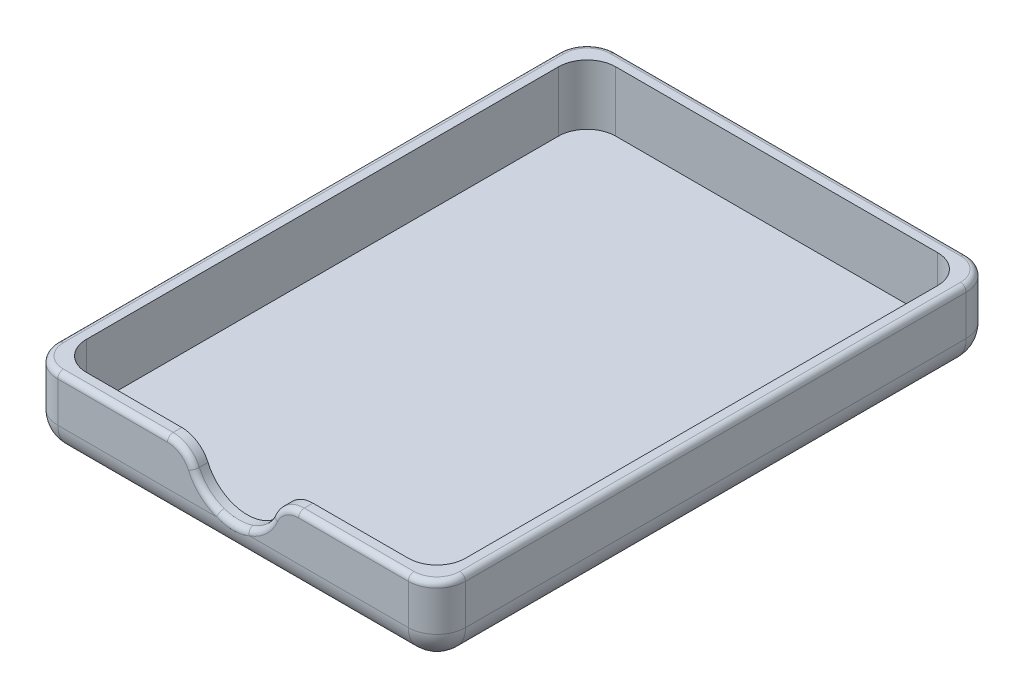
SolidWorks part; units mm, degrees
ref_plane "Front Plane" through (0, 0, 0) normal (0, 0, 1) x (1, 0, 0)
ref_plane "Top Plane" through (0, 0, 0) normal (0, 1, 0) x (1, 0, 0)
ref_plane "Right Plane" through (0, 0, 0) normal (1, 0, 0) x (0, 0, -1)
sketch "Sketch1" plane through (0, 0, 0) normal (0, 0, 1) x (1, 0, 0)
  line L0 (-71.25, -13) -> (71.25, -13)
  line L1 (71.25, -13) -> (71.25, 13)
  line L2 (71.25, 13) -> (-71.25, 13)
  line L3 (-71.25, 13) -> (-71.25, -13)
  arc A0 (15, 13) -> (-15, 13) centre (0, 13) cw
extrude "Boss-Extrude1" add sketch "Sketch1" against normal blind 5 contours L2 A0 L3 L0 L1
sketch "Sketch2" plane through (0, 0, -5) normal (0, 0, -1) x (-1, 0, 0)
  line L0 (-19.3649, 8) -> (-66.25, 8)
  line L1 (-66.25, 13) -> (-66.25, -8)
  line L2 (-66.25, -8) -> (66.25, -8)
  line L3 (66.25, -8) -> (66.25, 13)
  line L4 (66.25, 8) -> (19.3649, 8)
  line L5 (-15, 13) -> (-71.25, 13)
  line L6 (-71.25, 13) -> (-71.25, -13)
  line L7 (-71.25, -13) -> (71.25, -13)
  line L8 (71.25, -13) -> (71.25, 13)
  line L9 (71.25, 13) -> (15, 13)
  line L10 (-15, 13) -> (-71.25, 13)
  line L11 (-71.25, 13) -> (-71.25, -13)
  line L12 (-71.25, -13) -> (71.25, -13)
  line L13 (71.25, -13) -> (71.25, 13)
  line L14 (71.25, 13) -> (15, 13)
  line L15 (-66.25, 8) -> (-66.25, -8) construction
  line L16 (66.25, -8) -> (66.25, 8) construction
  arc A0 (-19.3649, 8) -> (19.3649, 8) centre (0, 13) ccw
  arc A1 (-15, 13) -> (15, 13) centre (0, 13) ccw
  arc A2 (-15, 13) -> (15, 13) centre (0, 13) ccw
  line M13 (-15, 13) -> (-71.25, 13)
  line M14 (-71.25, 13) -> (-71.25, -13)
  line M15 (-71.25, -13) -> (71.25, -13)
  line M16 (71.25, -13) -> (71.25, 13)
  line M17 (71.25, 13) -> (15, 13)
  dimension "D1" = 0
  dimension "D2" = 5
extrude "Boss-Extrude2" add sketch "Sketch2" along normal blind 185 contours L3 L2 L1 M13 M14 M15 M16 M17
sketch "Sketch3" plane through (0, 0, -190) normal (0, 0, -1) x (-1, 0, 0)
  line L0 (-66.25, -8) -> (66.25, -8) construction
  line L1 (66.25, -8) -> (66.25, 13) construction
  line L2 (66.25, 13) -> (15, 13) construction
  line L3 (-15, 13) -> (-66.25, 13) construction
  line L4 (-66.25, 13) -> (-66.25, -8) construction
  line L5 (66.25, 13) -> (66.25, -8) construction
  line L6 (66.25, -8) -> (-66.25, -8) construction
  line L7 (-66.25, -8) -> (-66.25, 13) construction
  line L8 (-66.25, 13) -> (-71.25, 13) construction
  line L9 (-71.25, 13) -> (-71.25, -13) construction
  line L10 (-71.25, -13) -> (71.25, -13) construction
  line L11 (71.25, -13) -> (71.25, 13) construction
  line L12 (71.25, 13) -> (66.25, 13) construction
  line L13 (-66.25, -8) -> (66.25, -8)
  line L14 (66.25, -8) -> (66.25, 13)
  line L15 (66.25, 13) -> (15, 13)
  line L16 (15, 13) -> (-66.25, 13)
  line L17 (-66.25, 13) -> (-66.25, -8)
  line L18 (66.25, 13) -> (66.25, -8)
  line L19 (66.25, -8) -> (-66.25, -8)
  line L20 (-66.25, -8) -> (-66.25, 13)
  line L21 (-66.25, 13) -> (-71.25, 13)
  line L22 (-71.25, 13) -> (-71.25, -13)
  line L23 (-71.25, -13) -> (71.25, -13)
  line L24 (71.25, -13) -> (71.25, 13)
  line L25 (71.25, 13) -> (66.25, 13)
  arc A0 (-15, 13) -> (15, 13) centre (0, 13) ccw construction
  arc A1 (-15, 13) -> (15, 13) centre (0, 13) ccw
  line M1 (66.25, 13) -> (66.25, -8)
  line M2 (66.25, -8) -> (-66.25, -8)
  line M3 (-66.25, -8) -> (-66.25, 13)
  line M4 (-66.25, 13) -> (-71.25, 13)
  line M5 (-71.25, 13) -> (-71.25, -13)
  line M6 (-71.25, -13) -> (71.25, -13)
  line M7 (71.25, -13) -> (71.25, 13)
  line M8 (71.25, 13) -> (66.25, 13)
extrude "Boss-Extrude3" add sketch "Sketch3" along normal blind 5 contours A1 L16 L15 M3 M2 M1 | L16 A1 | M8 M1 M2 M3 M4 M5 M6 M7
fillet "Fillet1" radius 10 14 edges at (-66.25, 2.5, -5) (66.25, 2.5, -5) (71.25, 0, -195) (-71.25, 0, -195) (-71.25, 0, 0) (71.25, 0, 0) (66.25, 2.5, -190) (-71.25, -13, -97.5) (-66.25, 2.5, -190) (71.25, -13, -97.5) (-15, 13, -2.5) (15, 13, -2.5) (0, -13, -195) (0, -13, 0)
fillet "Fillet2" radius 2 12 edges at (-68.3211, 13, -192.0711) (0, 13, -195) (68.3211, 13, -192.0711) (71.25, 13, -97.5) (68.3211, 13, -2.9289) (42.0814, 13, 0) (17.4357, 11.3666, 0) (0, -2, 0) (-17.4357, 11.3666, 0) (-42.0814, 13, 0) (-68.3211, 13, -2.9289) (-71.25, 13, -97.5)
sketch "Sketch4" plane through (0, 13, 0) normal (0, 1, 0) x (1, 0, 0)
  line L0 (-22.9129, 0) -> (-61.25, 0) construction
  line L1 (61.25, 0) -> (22.9129, 0) construction
  line L2 (71.25, 185) -> (71.25, 10) construction
  line L3 (-71.25, 10) -> (-71.25, 185) construction
  line L4 (-61.25, 195) -> (61.25, 195) construction
  line L5 (0, 0) -> (-71.25, 0) construction
  line L6 (71.25, 0) -> (0, 0) construction
  line L7 (71.25, 195) -> (71.25, 0) construction
  line L8 (-71.25, 0) -> (-71.25, 195) construction
  line L9 (-71.25, 195) -> (71.25, 195) construction
  point P0 (-70.6726, 0)
  point P2 (0, 0)
  point P4 (71.25, 0)
  point P7 (71.25, 195)
  point P10 (-71.25, 194.5387)
  point P13 (-71.25, 195)
  point P15 (71.25, 194.6134)
  point P18 (70.715, 0)
  point P22 (-0.8321, 0.0594)
sketch "Sketch5" plane through (71.25, 0, 0) normal (1, 0, 0) x (0, 0, -1)
  line L0 (0, 13) -> (0, -13) construction
  line L1 (0, 13) -> (195, 13) construction
  line L2 (185, -13) -> (10, -13) construction
  point P5 (0, 0)
